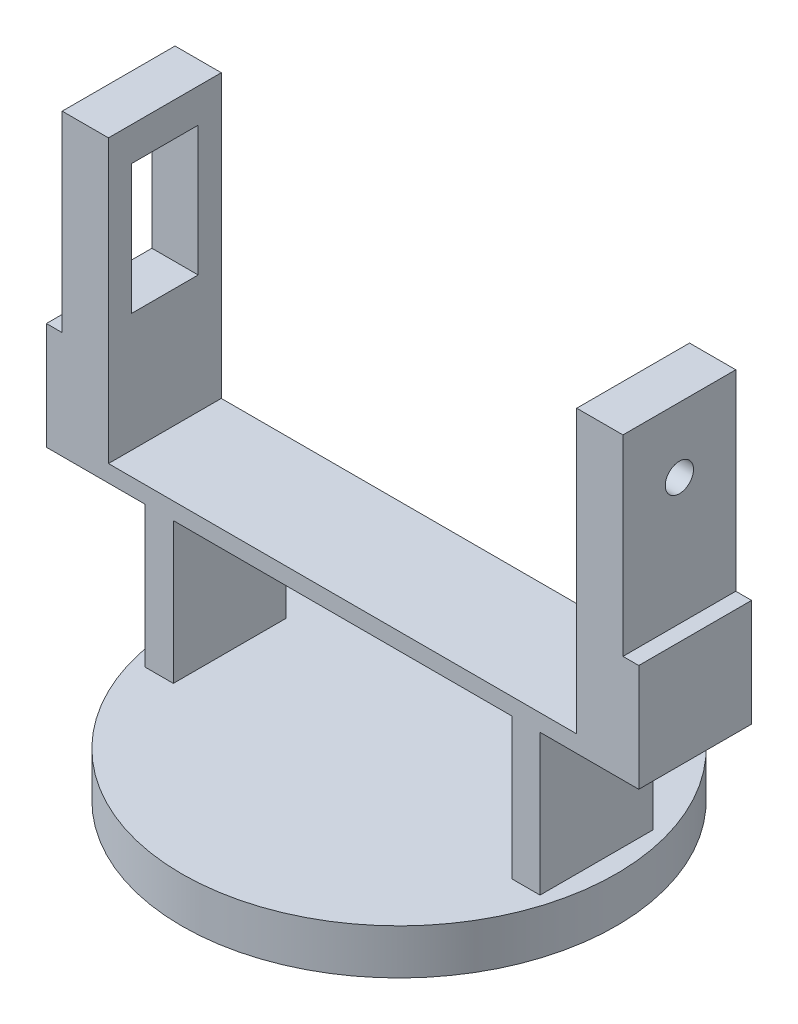
SolidWorks part; units mm, degrees
ref_plane "Front Plane" through (0, 0, 0) normal (0, 0, 1) x (1, 0, 0)
ref_plane "Top Plane" through (0, 0, 0) normal (0, 1, 0) x (1, 0, 0)
ref_plane "Right Plane" through (0, 0, 0) normal (1, 0, 0) x (0, 0, -1)
sketch "Sketch1" plane through (0, 0, 0) normal (0, 1, 0) x (1, 0, 0)
  circle A0 centre (0, 0) radius 38.5
  circle A1 centre (0, 0) radius 28.5
  dimension "D1" = 77
  dimension "D2" = 57
extrude "Boss-Extrude1" add sketch "Sketch1" along normal blind 3
sketch "Sketch3" plane through (0, 3, 0) normal (0, 1, 0) x (1, 0, 0)
  circle A0 centre (0, 0) radius 38.5
  dimension "D1" = 77
extrude "Boss-Extrude2" add sketch "Sketch3" along normal blind 5
sketch "Sketch4" plane through (0, 8, 0) normal (0, 1, 0) x (1, 0, 0)
  line L1 (-35, 10) -> (-30, 10)
  line L2 (-35, 10) -> (-35, -10)
  line L3 (-35, -10) -> (-30, -10)
  line L4 (-30, 10) -> (-30, -10)
  line L5 (30, 10) -> (35, 10)
  line L6 (30, 10) -> (30, -10)
  line L7 (30, -10) -> (35, -10)
  line L8 (35, 10) -> (35, -10)
  point P13 (-30, 0)
  dimension "D1" = 20
  dimension "D2" = 20
  dimension "D3" = 5
  dimension "D4" = 5
  dimension "D5" = 30
  dimension "D6" = 30
extrude "Boss-Extrude3" add sketch "Sketch4" along normal blind 25
sketch "Sketch5" plane through (0, 33, 0) normal (0, 1, 0) x (1, 0, 0)
  line L0 (35, 10) -> (30, 10) construction
  line L1 (-52.5, -10) -> (52.5, -10)
  line L2 (-52.5, -10) -> (-52.5, 10)
  line L3 (-52.5, 10) -> (52.5, 10)
  line L4 (52.5, -10) -> (52.5, 10)
  line L5 (30, -10) -> (35, -10) construction
  dimension "D1" = 105
  dimension "D2" = 52.5
extrude "Boss-Extrude4" add sketch "Sketch5" along normal blind 3
sketch "Sketch6" plane through (0, 36, 0) normal (0, 1, 0) x (1, 0, 0)
  line L0 (-52.5, -10) -> (52.5, -10) construction
  line L1 (-52.5, 10) -> (-49.7, 10)
  line L2 (-52.5, 10) -> (-52.5, -10)
  line L3 (-52.5, -10) -> (-49.7, -10)
  line L4 (-49.7, 10) -> (-49.7, -10)
  line L6 (52.5, 10) -> (49.7, 10)
  line L7 (52.5, 10) -> (52.5, -10)
  line L8 (52.5, -10) -> (49.7, -10)
  line L9 (49.7, 10) -> (49.7, -10)
  dimension "D1" = 2.8
  dimension "D2" = 2.8
extrude "Boss-Extrude5" add sketch "Sketch6" along normal blind 16
sketch "Sketch7" plane through (0, 36, 0) normal (0, 1, 0) x (1, 0, 0)
  line L0 (49.7, 10) -> (-49.7, 10) construction
  line L1 (-49.7, -10) -> (-41.5, -10)
  line L2 (-49.7, -10) -> (-49.7, 10)
  line L3 (-49.7, 10) -> (-41.5, 10)
  line L4 (-41.5, -10) -> (-41.5, 10)
  line L6 (49.7, -10) -> (41.5, -10)
  line L7 (49.7, -10) -> (49.7, 10)
  line L8 (49.7, 10) -> (41.5, 10)
  line L9 (41.5, -10) -> (41.5, 10)
  dimension "D1" = 8.2
  dimension "D2" = 8.2
extrude "Boss-Extrude6" add sketch "Sketch7" along normal blind 50
sketch "Sketch8" plane through (-49.7, 0, 0) normal (-1, 0, 0) x (0, 0, 1)
  line L0 (-10, 52) -> (10, 52) construction
  line L1 (-5.9, 57) -> (5.9, 57)
  line L2 (-5.9, 57) -> (-5.9, 80)
  line L3 (-5.9, 80) -> (5.9, 80)
  line L4 (5.9, 57) -> (5.9, 80)
  line L6 (-10, 86) -> (-10, 52) construction
  dimension "D1" = 23
  dimension "D2" = 11.8
  dimension "D3" = 5
  dimension "D4" = 4.1
extrude "Cut-Extrude1" cut sketch "Sketch8" against normal blind 50
sketch "Sketch9" plane through (41.5, 0, 0) normal (-1, 0, 0) x (0, 0, 1)
  line L0 (10, 52) -> (-10, 52) construction
  line L1 (10, 86) -> (10, 36) construction
  circle A0 centre (0, 74.47) radius 2.5
  dimension "D2" = 5
  dimension "D1" = 22.47
  dimension "D3" = 10
extrude "Cut-Extrude2" cut sketch "Sketch9" against normal blind 50
sketch "Sketch10" plane through (0, 3, 0) normal (0, -1, 0) x (1, 0, 0)
  line L0 (-36.102, 0) -> (36.102, 0) construction
  line L1 (0, 19.9749) -> (0, -19.9749) construction
  line L2 (2, 7.5) -> (2, 2.8874)
  line L3 (17.1176, 1.9965) -> (2, 2.8874)
  line L4 (17.1176, -1.9965) -> (2, -2.8874)
  line L5 (-17.1176, -1.9965) -> (-2, -2.8874)
  line L6 (-17.1176, 1.9965) -> (-2, 2.8874)
  line L7 (-2, 7.5) -> (-2, 2.8874)
  line L8 (2, -7.5) -> (2, -2.8874)
  line L9 (-2, -7.5) -> (-2, -2.8874)
  line L10 (-2, 2.8874) -> (-0.1765, 2.9948) construction
  line L11 (2, 2.8874) -> (0.1765, 2.9948) construction
  line L12 (2, -2.8874) -> (0.1765, -2.9948) construction
  line L13 (-2, -2.8874) -> (-0.1765, -2.9948) construction
  circle A0 centre (0, 0) radius 2
  arc A1 (17.1176, 1.9965) -> (17.1176, -1.9965) centre (17, 0) cw
  arc A2 (-2, 7.5) -> (2, 7.5) centre (0, 7.5) cw
  circle A3 centre (0, 0) radius 3 construction
  arc A4 (-17.1176, 1.9965) -> (-17.1176, -1.9965) centre (-17, 0) ccw
  arc A5 (-2, -7.5) -> (2, -7.5) centre (0, -7.5) ccw
  circle A6 centre (-17, 0) radius 0.5
  circle A7 centre (17, 0) radius 0.5
  circle A8 centre (-14.2852, -0.2685) radius 0.5
  circle A9 centre (-11.7852, -0.2685) radius 0.5
  circle A10 centre (-9.2852, -0.2685) radius 0.5
  circle A11 centre (-6.7852, -0.2685) radius 0.5
  circle A12 centre (-4.5, -0.2933) radius 0.5
  circle A13 centre (4.5, -0.2933) radius 0.5
  circle A14 centre (6.7852, -0.2685) radius 0.5
  circle A15 centre (9.2852, -0.2685) radius 0.5
  circle A16 centre (11.7852, -0.2685) radius 0.5
  circle A17 centre (14.2852, -0.2685) radius 0.5
  circle A18 centre (0, 7.5) radius 0.5
  circle A19 centre (0.1566, 4.4973) radius 0.5
  circle A20 centre (0.1566, -4.4973) radius 0.5
  circle A21 centre (0, -7.5) radius 0.5
  point P5 (0, 0)
  dimension "D1" = 4
  dimension "D3" = 2
  dimension "D5" = 2
  dimension "D6" = 6
  dimension "D7" = 1
  dimension "D9" = 1
  dimension "D2" = 17
  dimension "D4" = 7.5
  dimension "D8" = 4.6765
  dimension "D10" = 4.5
extrude "Cut-Extrude3" cut sketch "Sketch10" against normal blind 1 contours L2 L3 A1 L4 L8 A5 L9 L5 A4 L6 L7 A2 | A6 | A18 | A7 | A21
